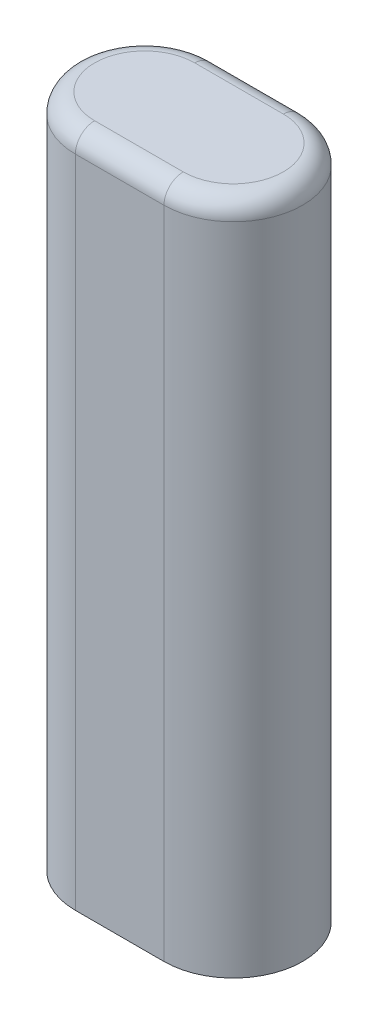
SolidWorks part; units mm, degrees
ref_plane "Front Plane" through (0, 0, 0) normal (0, 0, 1) x (1, 0, 0)
ref_plane "Top Plane" through (0, 0, 0) normal (0, 1, 0) x (1, 0, 0)
ref_plane "Right Plane" through (0, 0, 0) normal (1, 0, 0) x (0, 0, -1)
sketch "Sketch1" plane through (0, 0, 0) normal (0, 1, 0) x (1, 0, 0)
  line L0 (-1.4605, 0) -> (1.4605, 0) construction
  line L1 (-1.4605, 2.286) -> (1.4605, 2.286)
  line L2 (-1.4605, -2.286) -> (1.4605, -2.286)
  arc A0 (-1.4605, 2.286) -> (-1.4605, -2.286) centre (-1.4605, 0) ccw
  arc A1 (1.4605, -2.286) -> (1.4605, 2.286) centre (1.4605, 0) ccw
  point P2 (0, 0)
  dimension "D1" = 2.286
  dimension "D2" = 2.921
extrude "Boss-Extrude1" add sketch "Sketch1" along normal blind 22.225
fillet "Fillet1" radius 0.635 4 edges at (0, 22.225, 2.286) (-3.7465, 22.225, 0) (0, 22.225, -2.286) (3.7465, 22.225, 0)
sketch "Sketch2" plane through (0, 0, 0) normal (0, -1, 0) x (1, 0, 0)
  circle A0 centre (0, 0) radius 1.778
  dimension "D1" = 3.556
extrude "Cut-Extrude3" cut sketch "Sketch2" against normal blind 8.255
